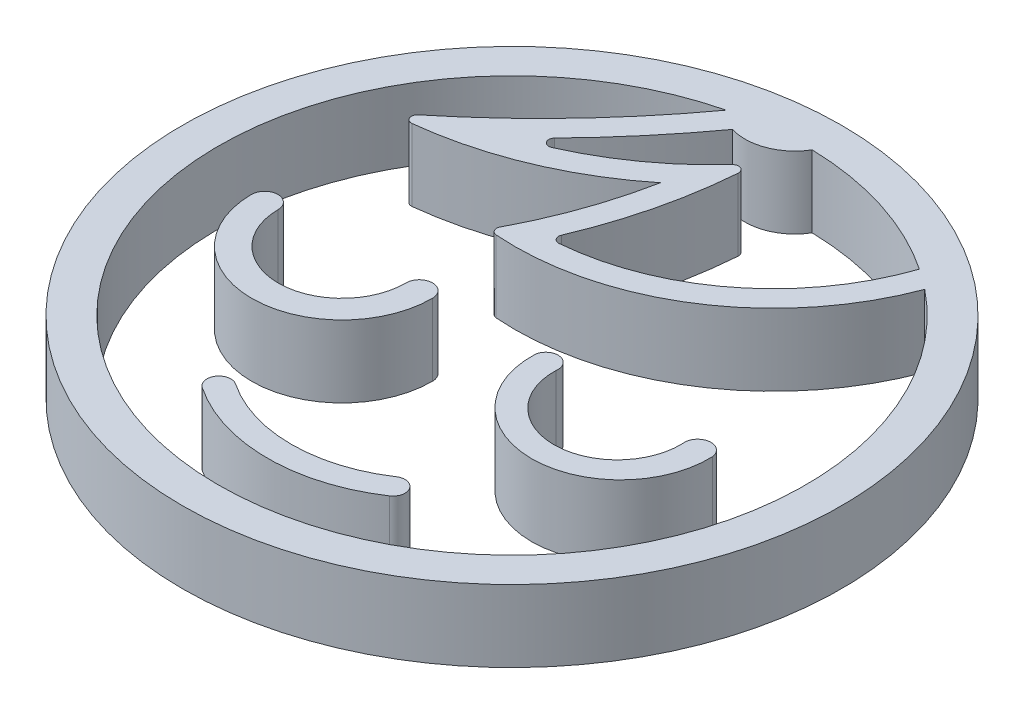
SolidWorks part; units mm, degrees
ref_plane "Alzado" through (0, 0, 0) normal (0, 0, 1) x (1, 0, 0)
ref_plane "Planta" through (0, 0, 0) normal (0, 1, 0) x (1, 0, 0)
ref_plane "Vista lateral" through (0, 0, 0) normal (1, 0, 0) x (0, 0, -1)
sketch "Croquis1" plane through (0, 0, 0) normal (0, 1, 0) x (1, 0, 0)
  line L0 (-8.3007, -65.0348) -> (191.6993, -65.0348) construction
  circle A0 centre (0, 0) radius 27.5
  arc A1 (15.3324, 19.1094) -> (-6.4819, 5.1617) centre (-4.873, 26.678) cw
  arc A2 (-3.3982, 15.7873) -> (-6.8868, 5.8937) centre (-38.63, 22.6486) cw
  arc A3 (-18.0355, 9.7052) -> (-3.3982, 15.7873) centre (-21.2019, 37.9801) ccw
  arc A4 (-18.4064, 10.5902) -> (-5.9012, 23.7787) centre (-62.7407, 65.1506) ccw
  arc A5 (3.7721, -1.8221) -> (18.5666, -1.8221) centre (11.1693, -2.1271) ccw
  arc A6 (16.3721, -2.1271) -> (5.8129, -2.1271) centre (11.0925, -2.3075) cw
  arc A7 (3.7721, -1.8221) -> (5.8129, -2.1271) centre (4.7925, -1.9746) cw
  arc A8 (18.5666, -1.8221) -> (16.3721, -2.1271) centre (17.4693, -1.9746) ccw
  arc A9 (-19.6178, -2.1324) -> (-4.5632, -2.0598) centre (-12.0905, -2.0961) ccw
  arc A10 (-17.4052, -2.1217) -> (-6.7758, -2.0705) centre (-12.0905, -2.0961) ccw
  arc A11 (-19.6178, -2.1324) -> (-17.4052, -2.1217) centre (-18.5115, -2.1271) cw
  arc A12 (-6.7758, -2.0705) -> (-4.5632, -2.0598) centre (-5.6695, -2.0652) cw
  arc A13 (-7.7057, -18.14) -> (7.9339, -18.14) centre (0.1141, -6.4787) ccw
  arc A14 (-6.5918, -16.4789) -> (6.82, -16.4789) centre (0.1141, -6.4787) ccw
  arc A15 (-6.5918, -16.4789) -> (-7.7057, -18.14) centre (-7.1487, -17.3095) ccw
  arc A16 (6.82, -16.4789) -> (7.9339, -18.14) centre (7.3769, -17.3095) cw
  arc A17 (13.6507, 20.3448) -> (-3.2376, 7.17) centre (-4.873, 26.678) cw
  arc A18 (-0.8501, 19.7141) -> (-3.7398, 7.8634) centre (-38.63, 22.6486) cw
  arc A19 (-10.4829, 13.7976) -> (-1.7169, 20.0909) centre (-21.2019, 37.9801) ccw
  arc A20 (-11.043, 14.6043) -> (-4.2484, 22.6509) centre (-62.7407, 65.1506) ccw
  arc A21 (-5.9012, 23.7787) -> (0.5539, 24.4937) centre (0, 0) ccw
  arc A22 (-6.0244, 23.7478) -> (-5.9667, 23.6888) centre (-3.0195, 26.6269) ccw
  arc A23 (15.5115, 19.6059) -> (-7.2448, 5.2323) centre (-4.873, 26.678) cw construction
  arc A24 (13.622, 20.2615) -> (-4.065, 7.1183) centre (-4.873, 26.678) cw construction
  arc A27 (-12.7506, 12.9149) -> (-4.2841, 22.6017) centre (-62.7407, 65.1506) ccw construction
  arc A28 (-4.2484, 22.6509) -> (0.5539, 24.4937) centre (-3.0195, 26.6269) ccw
  arc A29 (-0.7645, 21.1873) -> (-4.065, 7.1183) centre (-38.63, 22.6486) cw construction
  arc A30 (-3.2376, 7.17) -> (-3.7398, 7.8634) centre (-3.2794, 7.6683) cw
  arc A31 (-3.3982, 15.7873) -> (-7.2448, 5.2323) centre (-38.63, 22.6486) cw construction
  arc A32 (-6.4819, 5.1617) -> (-6.8868, 5.8937) centre (-6.4446, 5.6603) cw
  arc A33 (-19.6943, 9.5685) -> (-3.3982, 15.7873) centre (-21.2019, 37.9801) ccw construction
  arc A34 (-19.6943, 9.5685) -> (-5.9012, 23.7787) centre (-62.7407, 65.1506) ccw construction
  arc A35 (-18.0355, 9.7052) -> (-18.4064, 10.5902) centre (-18.0911, 10.2021) cw
  arc A36 (-12.7506, 12.9149) -> (-0.7645, 21.1873) centre (-21.2019, 37.9801) ccw construction
  arc A37 (-10.4829, 13.7976) -> (-11.043, 14.6043) centre (-10.6855, 14.2548) cw
  arc A38 (-0.8501, 19.7141) -> (-1.7169, 20.0909) centre (-1.3486, 19.7528) ccw
  arc A41 (-26.4032, -7.6889) -> (26.3995, -7.7018) centre (0, 0) ccw
  arc A44 (-26.4032, -7.6889) -> (26.3995, -7.7018) centre (0, 0) ccw
  arc A47 (27.167, 4.2668) -> (-27.1691, 4.2535) centre (0, 0) ccw
  point P53 (22, 0)
  point P79 (23.9076, 7.3093)
  dimension "D5" = 0.5
  dimension "D6" = 0.5
  dimension "D2" = 2
  dimension "D3" = 2
extrude "Saliente-Extruir3" add sketch "Croquis1" along normal blind 6
